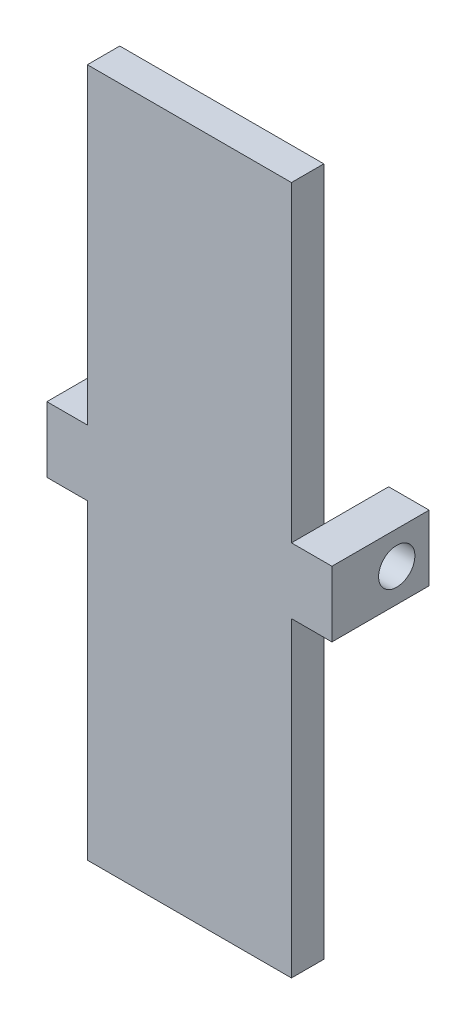
SolidWorks part; units mm, degrees
ref_plane "Front Plane" through (0, 0, 0) normal (0, 0, 1) x (1, 0, 0)
ref_plane "Top Plane" through (0, 0, 0) normal (0, 1, 0) x (1, 0, 0)
ref_plane "Right Plane" through (0, 0, 0) normal (1, 0, 0) x (0, 0, -1)
sketch "Sketch1" plane through (0, 0, 0) normal (0, 0, 1) x (1, 0, 0)
  line L4 (0, 0) -> (-16, 0)
  line L5 (0, 54.0113) -> (0, 0)
  line L6 (-16, 54.0113) -> (-16, 0)
  line L7 (0, 54.0113) -> (-16, 54.0113)
  dimension "D1" = 54.0113
  dimension "D2" = 16
extrude "Boss-Extrude1" add sketch "Sketch1" along normal blind 2.54
sketch "Sketch2" plane through (0, 0, 0) normal (1, 0, 0) x (0, 0, -1)
  line L0 (-2.54, 27.0057) -> (20.0792, 27.0057) construction
  line L2 (-2.54, 0) -> (-2.54, 54.0113) construction
  line L3 (0, 0) -> (0, 54.0113) construction
  line L4 (-2.54, 24.4042) -> (5.08, 24.4042)
  line L5 (5.08, 24.4042) -> (5.08, 29.5457)
  line L6 (5.08, 29.5457) -> (-2.54, 29.5457)
  line L7 (-2.54, 29.5457) -> (-2.54, 24.4042)
  circle A0 centre (2.54, 27.0057) radius 1.4224
  dimension "D1" = 5.1415
  dimension "0.112" = 2.8448
  dimension "0.1" = 2.54
  dimension "0.20" = 5.08
  dimension "0.10" = 2.54
extrude "Boss-Extrude2" add sketch "Sketch2" along normal blind 3.175
sketch "Sketch3" plane through (0, 0, 0) normal (0, -1, 0) x (1, 0, 0)
  line L0 (-8, 0) -> (-8, 16.7161) construction
  line L1 (-16, 0) -> (0, 0) construction
ref_plane "Plane1" through (-8, 0, 0) normal (-1, 0, 0) x (0, 0, 1)
mirror "Mirror1" about plane through (-8, 0, 0) normal (-1, 0, 0) of "Boss-Extrude2"
